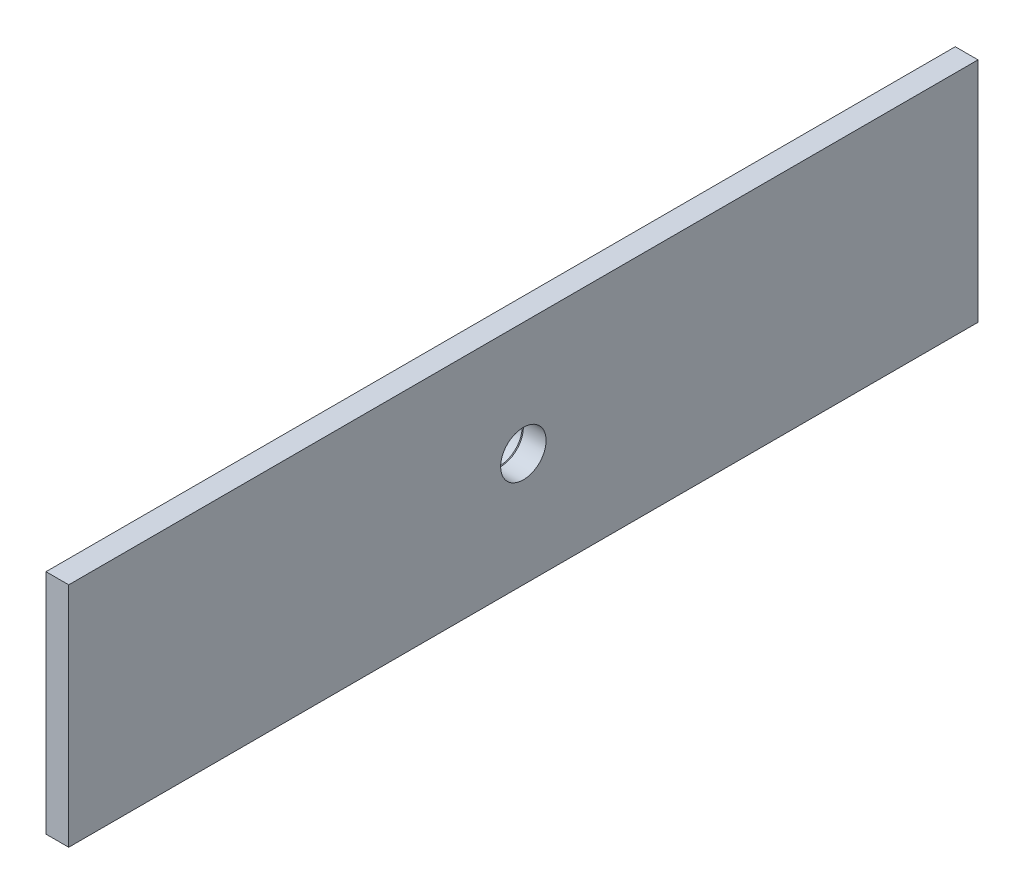
SolidWorks part; units mm, degrees
ref_plane "Front Plane" through (0, 0, 0) normal (0, 0, 1) x (1, 0, 0)
ref_plane "Top Plane" through (0, 0, 0) normal (0, 1, 0) x (1, 0, 0)
ref_plane "Right Plane" through (0, 0, 0) normal (1, 0, 0) x (0, 0, -1)
ref_plane "Plane1" through (0, 0, 889.1) normal (0, 0, 1) x (1, 0, 0)
sketch "Sketch1" plane through (0, 0, 889.1) normal (0, 0, 1) x (1, 0, 0)
  line L0 (528, 20) -> (528, 0)
  line L1 (528, 0) -> (533, 0)
  line L2 (533, 0) -> (533, 20)
  line L3 (533, 20) -> (528, 20)
  line L4 (528, 0) -> (533, 0) construction
revolve "Revolve1" add sketch "Sketch1" angle 360 about L4
imported_body "Surface-Imported1"
ref_plane "Plane2" through (0, 0, 908.9) normal (0, 0, -1) x (-1, 0, 0)
sketch "Sketch2" plane through (0, 0, 908.9) normal (0, 0, -1) x (-1, 0, 0)
  line L0 (-528.5, 0.5) -> (-530.5, 0.5)
  line L1 (-530.5, 0.5) -> (-530.5, -0.5)
  line L2 (-530.5, -0.5) -> (-528.5, -0.5)
  line L3 (-528.5, -0.5) -> (-528.5, 0.5)
extrude "Cut-Extrude1" cut sketch "Sketch2" against normal up to surface
hole_wizard "Ø20.0 (20) Diameter Hole1" positions "Sketch4" profile "Sketch3" hole size "Ø20.0" standard "ANSI Metric"
sketch "Sketch4" plane through (533, 0, 0) normal (1, 0, 0) x (0, 0, -1)
  point P0 (-889.1, 0)
sketch "Sketch3" plane through (533, 0, 889.1) normal (0, 1, 0) x (0, 0, -1)
  line L0 (0, 0) -> (0, 5)
  line L1 (0, 5) -> (10, 5)
  line L2 (10, 5) -> (10, 0)
  line L5 (10, 0) -> (0, 0)
  line L11 (0, -6.35) -> (0, 107.95) construction
  dimension "Thru Hole Dia." = 20
  dimension "Thru Hole Depth" = 5
hole_wizard "Ø5.0 (5) Diameter Hole1" positions "Sketch6" profile "Sketch5" hole size "Ø5.0" standard "ANSI Metric"
sketch "Sketch6" plane through (528, 0, 0) normal (-1, 0, 0) x (0, 0, 1)
  point P0 (904.85, 0)
sketch "Sketch5" plane through (528, 0, 904.85) normal (0, 1, 0) x (0, 0, 1)
  line L0 (0, 0) -> (0, 5)
  line L1 (0, 5) -> (2.5, 5)
  line L2 (2.5, 5) -> (2.5, 0)
  line L5 (2.5, 0) -> (0, 0)
  line L11 (0, -6.35) -> (0, 107.95) construction
  dimension "Thru Hole Dia." = 5
  dimension "Thru Hole Depth" = 5
hole_wizard "Ø4.2 (4.2) Diameter Hole1" positions "Sketch8" profile "Sketch7" hole size "Ø4.2" standard "ANSI Metric"
sketch "Sketch8" plane through (528, 0, 0) normal (-1, 0, 0) x (0, 0, 1)
  point P0 (900.2369, 11.1369)
  point P1 (877.9631, -11.1369)
  point P2 (877.9631, 11.1369)
  point P3 (900.2369, -11.1369)
sketch "Sketch7" plane through (528, 11.1369, 900.2369) normal (0, 1, 0) x (0, 0, 1)
  line L0 (0, 0) -> (0, 5)
  line L1 (0, 5) -> (2.1, 5)
  line L2 (2.1, 5) -> (2.1, 0)
  line L5 (2.1, 0) -> (0, 0)
  line L11 (0, -6.35) -> (0, 107.95) construction
  dimension "Thru Hole Dia." = 4.2
  dimension "Thru Hole Depth" = 5
chamfer "Chamfer1" distance 0.5 angle 60 1 edges at (533, 20, 889.1)
chamfer "Chamfer2" distance 0.5 angle 45 1 edges at (533, 0, 879.1)
sketch "Sketch9" plane through (533, 0, 0) normal (1, 0, 0) x (0, 0, -1)
  line L1 (-1089.1, 50) -> (-689.1, 50)
  line L2 (-1089.1, 50) -> (-1089.1, -50)
  line L3 (-1089.1, -50) -> (-689.1, -50)
  line L4 (-689.1, 50) -> (-689.1, -50)
  circle A0 centre (-889.1, 0) radius 10
  dimension "D1" = 200
  dimension "D2" = 200
  dimension "D3" = 100
  dimension "D4" = 50
extrude "Boss-Extrude1" add sketch "Sketch9" along normal blind 10
